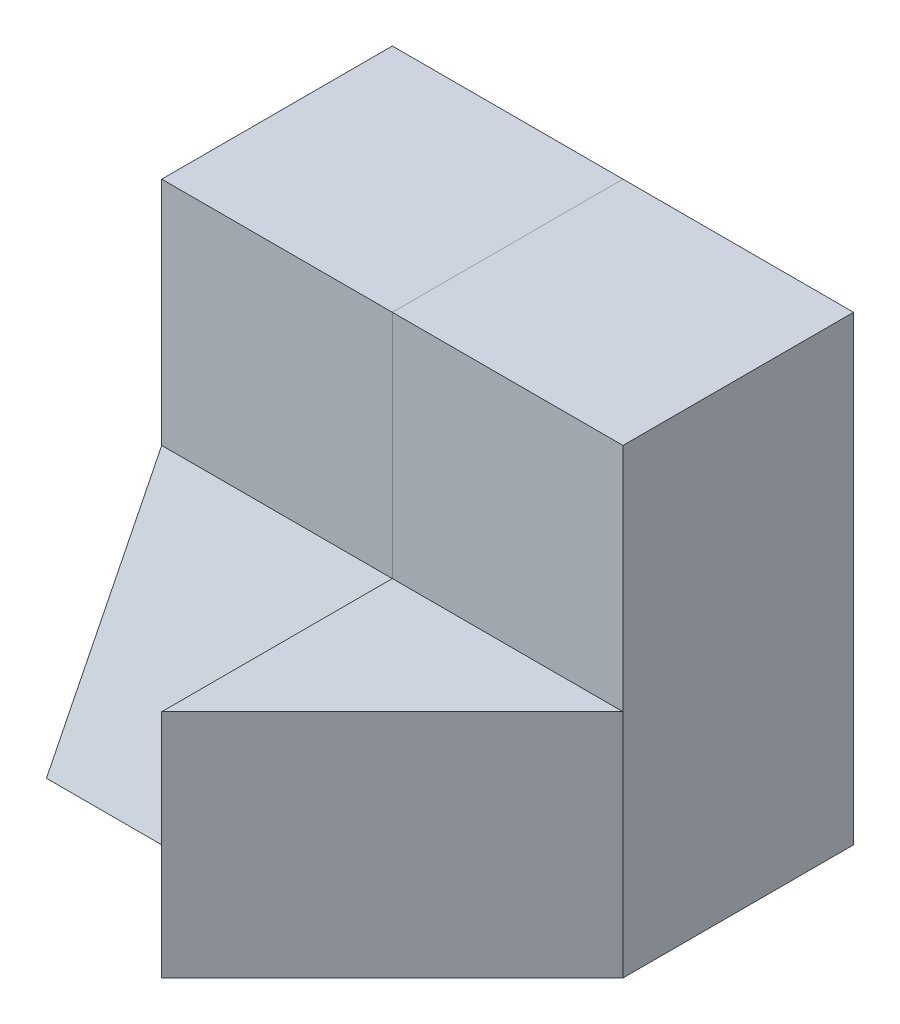
SolidWorks part; units mm, degrees
ref_plane "Front Plane" through (0, 0, 0) normal (0, 0, 1) x (1, 0, 0)
ref_plane "Top Plane" through (0, 0, 0) normal (0, 1, 0) x (1, 0, 0)
ref_plane "Right Plane" through (0, 0, 0) normal (1, 0, 0) x (0, 0, -1)
sketch "Sketch1" plane through (0, 0, 0) normal (0, 0, 1) x (1, 0, 0)
  line L1 (0, 0) -> (40, 0)
  line L2 (0, 0) -> (0, 40)
  line L3 (0, 40) -> (40, 40)
  line L4 (40, 0) -> (40, 40)
  dimension "D1" = 40
  dimension "D2" = 40
extrude "Boss-Extrude1" add sketch "Sketch1" along normal blind 40
sketch "Sketch2" plane through (0, 40, 0) normal (0, 1, 0) x (1, 0, 0)
  line L1 (0, -40) -> (20, -40)
  line L2 (0, -40) -> (0, -30)
  line L3 (0, -30) -> (20, -30)
  line L4 (20, -40) -> (20, -30)
  dimension "D1" = 20
  dimension "D2" = 10
extrude "Cut-Extrude1" cut sketch "Sketch2" against normal blind 40
sketch "Sketch3" plane through (0, 0, 0) normal (-1, 0, 0) x (0, 0, 1)
  line L0 (20, 40) -> (20, 20)
  line L1 (30, 40) -> (0, 40) construction
  line L2 (20, 20) -> (40, 20)
  line L3 (40, 20) -> (40, 40)
  line L4 (40, 40) -> (20, 40)
  dimension "D1" = 20
  dimension "D2" = 20
  dimension "D3" = 20
extrude "Cut-Extrude2" cut sketch "Sketch3" against normal blind 40
sketch "Sketch5" plane through (40, 0, 0) normal (1, 0, 0) x (0, 0, -1)
  line L1 (-20, 20) -> (-40, 20)
  line L2 (-20, 20) -> (-20, 0)
  line L3 (-20, 0) -> (-40, 0)
  line L4 (-40, 20) -> (-40, 0)
extrude "Cut-Extrude3" cut sketch "Sketch5" against normal blind 10
sketch "Sketch7" plane through (0, 0, 20) normal (0, 0, 1) x (1, 0, 0)
  line L0 (40, 40) -> (0, 40) construction
  line L1 (0, 20) -> (20, 20)
  line L2 (0, 20) -> (0, 40)
  line L3 (0, 40) -> (20, 40)
  line L4 (20, 20) -> (20, 40)
extrude "Boss-Extrude2" add sketch "Sketch7" along normal blind 10
sketch "Sketch8" plane through (30, 0, 0) normal (1, 0, 0) x (0, 0, -1)
  line L1 (-20, 20) -> (-40, 20)
  line L2 (-20, 20) -> (-20, 0)
  line L3 (-20, 0) -> (-40, 0)
  line L4 (-40, 20) -> (-40, 0)
extrude "Boss-Extrude3" add sketch "Sketch8" along normal blind 10
sketch "Sketch10" plane through (0, 20, 0) normal (0, 1, 0) x (1, 0, 0)
  line L0 (20, -40) -> (40, -20)
  line L1 (40, -20) -> (40, -40)
  line L2 (40, -40) -> (20, -40)
extrude "Cut-Extrude10" cut sketch "Sketch10" against normal blind 27
sketch "Sketch11" plane through (0, 0, 0) normal (-1, 0, 0) x (0, 0, 1)
  line L0 (10.0001, 39.9999) -> (0.0001, 0)
  line L1 (10.0001, 39.9999) -> (30.0001, 0)
  line L2 (30.0001, 0) -> (0.0001, 0)
  dimension "D1" = 10
  dimension "D2" = 20
  dimension "D3" = 0.0001
  dimension "D4" = 0.0001
  dimension "D5" = 0.0001
extrude "Cut-Extrude12" cut sketch "Sketch11" against normal blind 20
sketch "Sketch12" plane through (0, 40, 0) normal (0, 1, 0) x (1, 0, 0)
  line L1 (40, 0) -> (20, 0)
  line L2 (40, 0) -> (40, -20)
  line L3 (40, -20) -> (20, -20)
  line L4 (20, 0) -> (20, -20)
extrude "Boss-Extrude4" add sketch "Sketch12" along normal blind 0.0001
sketch "Sketch14" plane through (0, 0, 0) normal (-1, 0, 0) x (0, 0, 1)
  line L1 (30, 40) -> (20.001, 40)
  line L2 (30, 40) -> (30, 20.001)
  line L3 (30, 20.001) -> (20.001, 20.001)
  line L4 (20.001, 40) -> (20.001, 20.001)
  dimension "D1" = 9.999
  dimension "D2" = 19.999
extrude "Cut-Extrude19" cut sketch "Sketch14" against normal blind 20.0001
sketch "Sketch15" plane through (0, 0, 0) normal (-1, 0, 0) x (0, 0, 1)
  line L0 (20.001, 20.001) -> (30, 20.001)
  line L1 (30, 20.001) -> (30, 0.0002)
  line L2 (30, 0.0002) -> (20.001, 20.001)
extrude "Cut-Extrude20" cut sketch "Sketch15" against normal blind 20.0001
sketch "Sketch16" plane through (20, 0, 0) normal (-1, 0, 0) x (0, 0, 1)
  line L0 (40, 20) -> (20.001, 20.001)
  line L1 (20.001, 20.001) -> (30, 0.0002)
  line L2 (30, 0.0002) -> (40, 0)
  line L3 (40, 0) -> (40, 20)
extrude "Cut-Extrude21" cut sketch "Sketch16" against normal blind 0.0001
